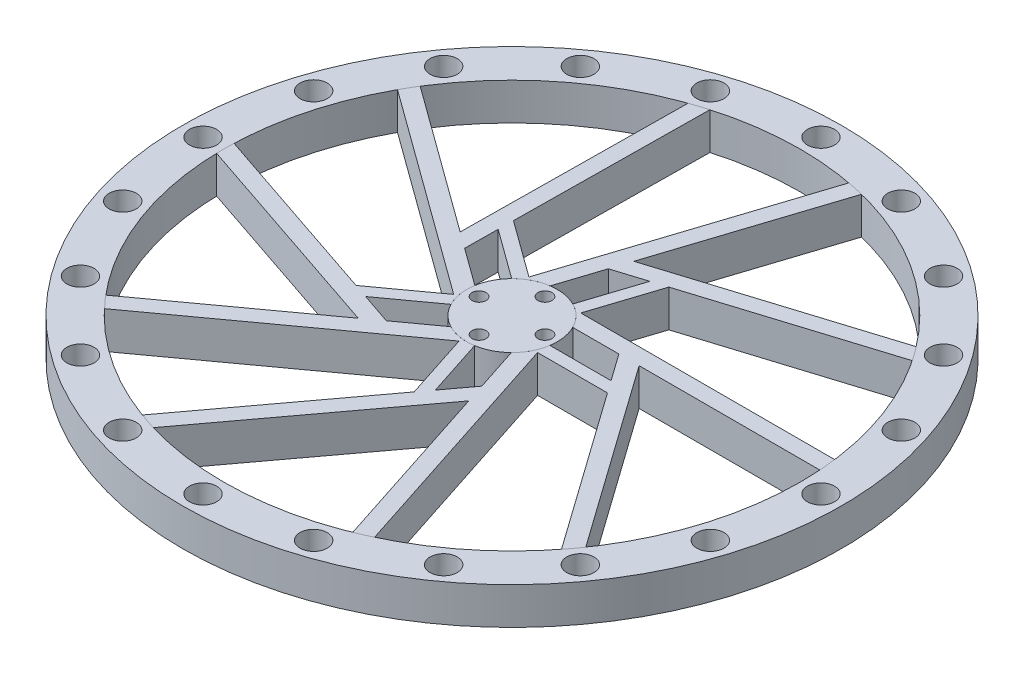
SolidWorks part; units mm, degrees
ref_plane "Front Plane" through (0, 0, 0) normal (0, 0, 1) x (1, 0, 0)
ref_plane "Top Plane" through (0, 0, 0) normal (0, 1, 0) x (1, 0, 0)
ref_plane "Right Plane" through (0, 0, 0) normal (1, 0, 0) x (0, 0, -1)
sketch "Sketch2" plane through (0, 0, 0) normal (0, 1, 0) x (1, 0, 0)
  circle A0 centre (0, 0) radius 80
  circle A1 centre (0, 0) radius 11
  circle A2 centre (0, 0) radius 70
  dimension "D1" = 160
  dimension "D2" = 22
  dimension "D3" = 10
extrude "Boss-Extrude2" add sketch "Sketch2" along normal blind 9 contours A2 | A0 | A1
sketch "Sketch3" plane through (0, 0, 0) normal (0, 1, 0) x (1, 0, 0)
  line L0 (-10.4616, -3.3992) -> (-61.4025, 33.6115)
  line L1 (0, -11) -> (10.4616, -3.3992) construction
  line L2 (10.4616, -3.3992) -> (6.4656, 8.8992) construction
  line L3 (6.4656, 8.8992) -> (-6.4656, 8.8992) construction
  line L4 (-6.4656, 8.8992) -> (-10.4616, -3.3992) construction
  line L5 (-10.4616, -3.3992) -> (0, -11) construction
  line L6 (-6.4656, 8.8992) -> (12.992, 68.7838)
  line L7 (6.4656, 8.8992) -> (69.432, 8.8992)
  line L8 (10.4616, -3.3992) -> (29.9193, -63.2838)
  line L9 (0, -11) -> (-50.9409, -48.0107)
  line L10 (-5.0881, -9.7525) -> (-53.6126, -45.0076)
  line L11 (-10.8475, 1.8254) -> (-59.372, 37.0805)
  line L12 (-1.616, 10.8807) -> (16.9187, 67.9246)
  line L13 (9.8488, 4.8992) -> (69.8283, 4.8992)
  line L14 (7.7028, -7.8528) -> (26.2375, -64.8968)
  line L15 (3.3608, 26.1977) -> (55.5948, 42.535)
  line L16 (2.6262, 23.9368) -> (-1.616, 10.8807)
  line L17 (9.8488, 4.8992) -> (23.5768, 4.8992) construction
  line L18 (7.7028, -7.8528) -> (11.945, -20.9089) construction
  line L19 (-5.0881, -9.7525) -> (-16.1944, -17.8216) construction
  line L20 (-10.8475, 1.8254) -> (-21.9537, 9.8946) construction
  line L21 (1.845, 21.5325) -> (58.0533, 39.1128)
  line L22 (3.2953, 21.9861) -> (56.7888, 38.7173) construction
  line L23 (21.0488, 4.8992) -> (55.138, -43.1254)
  line L24 (25.954, 4.8992) -> (57.6329, -39.7297)
  line L25 (11.1638, -18.5046) -> (-23.9762, -65.7658)
  line L26 (12.6796, -23.1698) -> (-19.9757, -67.0893)
  line L27 (-14.1491, -16.3357) -> (-69.9561, 2.4799)
  line L28 (-18.1176, -19.2189) -> (-69.9785, -1.7337)
  line L29 (-19.9085, 8.4086) -> (-19.2591, 67.2985)
  line L30 (-23.8769, 11.2919) -> (-23.2734, 66.0178)
  line L31 (9.5286, 23.9357) -> (4.9442, 9.8262)
  line L32 (13.0399, 25.0339) -> (7.7974, 8.8992)
  line L33 (12.3709, 22.9751) -> (7.7974, 8.8992) construction
  line L34 (9.5177, 23.9022) -> (4.9442, 9.8262) construction
  line L35 (27.8382, -4.6657) -> (10.8731, -4.6657)
  line L36 (25.7087, -1.6657) -> (10.8731, -1.6657)
  line L37 (4.1651, -27.9175) -> (-1.0774, -11.7828)
  line L38 (6.3602, -24.9652) -> (1.7758, -10.8557)
  line L39 (-25.264, -12.5882) -> (-11.539, -2.6164)
  line L40 (-21.7779, -13.7636) -> (-9.7757, -5.0435)
  line L41 (-19.7791, 20.1376) -> (-6.0541, 10.1657)
  line L42 (-19.8197, 16.4588) -> (-7.8175, 7.7387)
  line L43 (2.1012, 25.8037) -> (55.5948, 42.535) construction
  line L44 (-2.6614, 7.6631) -> (16.7963, 67.5477) construction
  line L45 (-8.1105, -0.1631) -> (-59.0513, 36.8476) construction
  line L46 (-2.3511, -7.7639) -> (-53.292, -44.7746) construction
  line L47 (6.6574, -4.6353) -> (26.1151, -64.5198) construction
  line L48 (6.4656, 4.8992) -> (69.432, 4.8992) construction
  circle A0 centre (0, 0) radius 70 construction
  circle A1 centre (0, 0) radius 11 construction
  arc A2 (55.138, -43.1254) -> (57.6329, -39.7297) centre (0, 0) ccw
  circle A3 centre (0, 0) radius 11
  circle A4 centre (0, 0) radius 8.8992 construction
  circle A5 centre (0, 0) radius 11
  circle A6 centre (0, 0) radius 11
  circle A7 centre (0, 0) radius 11
  circle A8 centre (0, 0) radius 11
  circle A9 centre (0, 0) radius 11
  circle A10 centre (0, 0) radius 11
  circle A11 centre (0, 0) radius 11
  circle A12 centre (0, 0) radius 11
  arc A13 (69.8283, 4.8992) -> (69.432, 8.8992) centre (0, 0) ccw
  arc A14 (58.0533, 39.1128) -> (55.5948, 42.535) centre (0, 0) ccw
  arc A15 (16.9187, 67.9246) -> (12.992, 68.7838) centre (0, 0) ccw
  arc A16 (-19.2591, 67.2985) -> (-23.2734, 66.0178) centre (0, 0) ccw
  arc A17 (-59.372, 37.0805) -> (-61.4025, 33.6115) centre (0, 0) ccw
  arc A18 (-69.9561, 2.4799) -> (-69.9785, -1.7337) centre (0, 0) ccw
  arc A19 (-53.6126, -45.0076) -> (-50.9409, -48.0107) centre (0, 0) ccw
  arc A20 (-23.9762, -65.7658) -> (-19.9757, -67.0893) centre (0, 0) ccw
  arc A21 (26.2375, -64.8968) -> (29.9193, -63.2838) centre (0, 0) ccw
  point P60 (0, 0)
  point P86 (0, 0)
  dimension "D1" = 4
  dimension "D2" = 4
  dimension "D3" = 24
  dimension "D5" = 3
  dimension "D4" = 5
  dimension "D6" = 5
extrude "Boss-Extrude5" add sketch "Sketch3" along normal mid plane 9 from offset 4.5 separate body contours L21 A14 L15 L12 L16 | L13 A13 L7 A3 | L23 A2 L24 L13 | A3 L8 L35 L23 L36 | L14 A21 L8 A3 | L25 A20 L26 L14 | A3 L9 L37 L25 L38 | L10 A19 L9 A3 | L27 A18 L28 L10 | A3 L0 L39 L27 L40 | L11 A17 L0 A3 | A3 L6 L41 L29 L42 | L29 A16 L30 L11 | L12 A15 L6 A3 L16 | A3 L7 L32 L21 L31
sketch "Sketch4" plane through (0, 9, 0) normal (0, 1, 0) x (1, 0, 0)
  circle A0 centre (0, 0) radius 8 construction
  circle A1 centre (0, 8) radius 1.5
  circle A2 centre (8, 0) radius 1.5
  circle A3 centre (0, -8) radius 1.5
  circle A4 centre (-8, 0) radius 1.5
  point P14 (0, 0)
  dimension "D1" = 4
sketch "Sketch5" plane through (0, 9, 0) normal (0, 1, 0) x (1, 0, 0)
  line L0 (0, 80) -> (0, 70) construction
  circle A0 centre (0, 0) radius 80 construction
  circle A1 centre (0, 0) radius 70 construction
  circle A2 centre (0, 75) radius 3
  circle A3 centre (23.1763, 71.3292) radius 3
  circle A4 centre (44.0839, 60.6763) radius 3
  circle A5 centre (60.6763, 44.0839) radius 3
  circle A6 centre (71.3292, 23.1763) radius 3
  circle A7 centre (75, 0) radius 3
  circle A8 centre (71.3292, -23.1763) radius 3
  circle A9 centre (60.6763, -44.0839) radius 3
  circle A10 centre (44.0839, -60.6763) radius 3
  circle A11 centre (23.1763, -71.3292) radius 3
  circle A12 centre (0, -75) radius 3
  circle A13 centre (-23.1763, -71.3292) radius 3
  circle A14 centre (-44.0839, -60.6763) radius 3
  circle A15 centre (-60.6763, -44.0839) radius 3
  circle A16 centre (-71.3292, -23.1763) radius 3
  circle A17 centre (-75, 0) radius 3
  circle A18 centre (-71.3292, 23.1763) radius 3
  circle A19 centre (-60.6763, 44.0839) radius 3
  circle A20 centre (-44.0839, 60.6763) radius 3
  circle A21 centre (-23.1763, 71.3292) radius 3
  point P10 (0, 75)
  point P59 (0, 0)
  dimension "D1" = 20
hole_wizard "M6 Clearance Hole1" positions "3DSketch1" profile "Sketch6" hole size "M6" standard "ANSI Metric"
sketch3d "3DSketch1"
  point P0 (-23.1763, 9, 71.3292)
  point P3 (0, 9, 75)
  point P6 (23.1763, 9, 71.3292)
  point P9 (44.0839, 9, 60.6763)
  point P12 (60.6763, 9, 44.0839)
  point P15 (71.3292, 9, 23.1763)
  point P18 (75, 9, 0)
  point P21 (71.3292, 9, -23.1763)
  point P24 (60.6763, 9, -44.0839)
  point P27 (44.0839, 9, -60.6763)
  point P30 (23.1763, 9, -71.3292)
  point P33 (0, 9, -75)
  point P36 (-23.1763, 9, -71.3292)
  point P39 (-44.0839, 9, -60.6763)
  point P42 (-60.6763, 9, -44.0839)
  point P45 (-71.3292, 9, -23.1763)
  point P48 (-75, 9, 0)
  point P51 (-71.3292, 9, 23.1763)
  point P54 (-60.6763, 9, 44.0839)
  point P57 (-44.0839, 9, 60.6763)
sketch "Sketch6" plane through (-23.1763, 9, 71.3292) normal (1, 0, 0) x (0, 0, 1)
  line L0 (0, 0) -> (0, 11.9828)
  line L1 (0, 11.9828) -> (3.3, 10)
  line L2 (3.3, 10) -> (3.3, 0)
  line L5 (3.3, 0) -> (0, 0)
  line L10 (0, 11.9828) -> (-3.3, 10) construction
  line L11 (0, -6.35) -> (0, 107.95) construction
  dimension "Hole Dia." = 6.6
  dimension "Hole Depth" = 10
  dimension "Drill Angle" = 118
hole_wizard "M3 Clearance Hole1" positions "3DSketch2" profile "Sketch7" hole size "M3" standard "ANSI Metric"
sketch3d "3DSketch2"
  point P0 (8, 9, 0)
  point P3 (0, 9, 8)
  point P6 (-8, 9, 0)
  point P9 (0, 9, -8)
sketch "Sketch7" plane through (8, 9, 0) normal (1, 0, 0) x (0, 0, 1)
  line L0 (0, 0) -> (0, 11.0215)
  line L1 (0, 11.0215) -> (1.7, 10)
  line L2 (1.7, 10) -> (1.7, 0)
  line L5 (1.7, 0) -> (0, 0)
  line L10 (0, 11.0215) -> (-1.7, 10) construction
  line L11 (0, -6.35) -> (0, 107.95) construction
  dimension "Hole Dia." = 3.4
  dimension "Hole Depth" = 10
  dimension "Drill Angle" = 118
